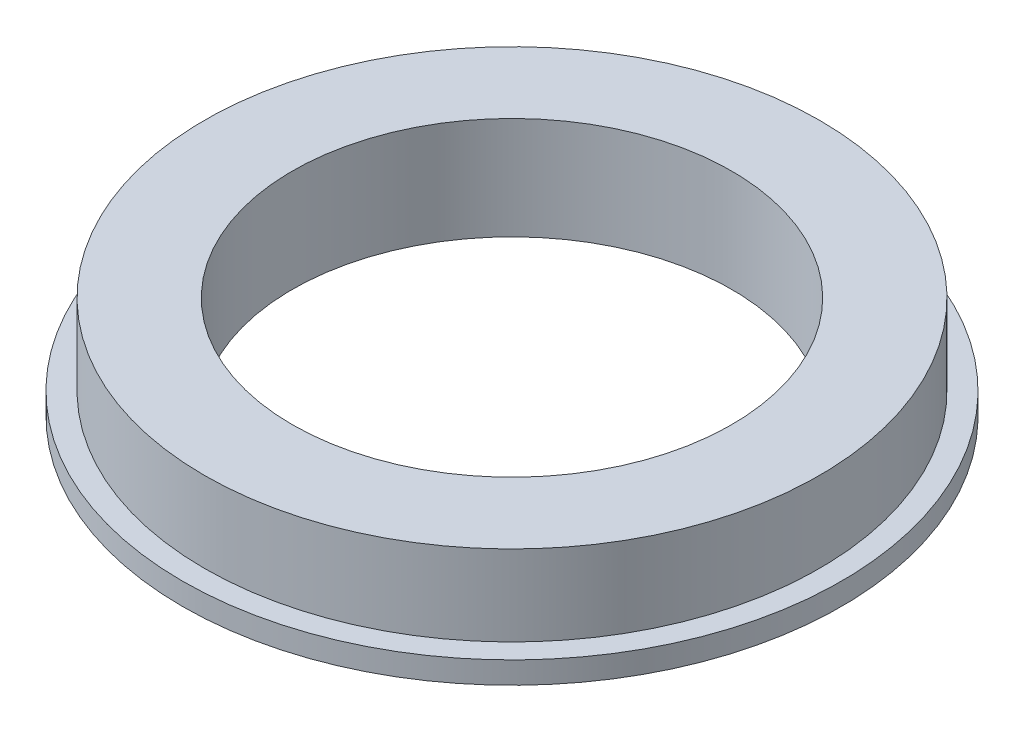
SolidWorks part; units mm, degrees
ref_plane "前视基准面" through (0, 0, 0) normal (0, 0, 1) x (1, 0, 0)
ref_plane "上视基准面" through (0, 0, 0) normal (0, 1, 0) x (1, 0, 0)
ref_plane "右视基准面" through (0, 0, 0) normal (1, 0, 0) x (0, 0, -1)
sketch "草图1" plane through (0, 0, 0) normal (0, 1, 0) x (1, 0, 0)
  circle A0 centre (0, 0) radius 22.5
  dimension "D1" = 45
extrude "凸台-拉伸1" add sketch "草图1" along normal blind 1.5
sketch "草图2" plane through (0, 1.5, 0) normal (0, 1, 0) x (1, 0, 0)
  circle A0 centre (0, 0) radius 21
  dimension "D1" = 42
extrude "凸台-拉伸2" add sketch "草图2" along normal blind 5.5
sketch "草图3" plane through (0, 7, 0) normal (0, 1, 0) x (1, 0, 0)
  circle A0 centre (0, 0) radius 15
  dimension "D1" = 30
extrude "切除-拉伸1" cut sketch "草图3" against normal through all
